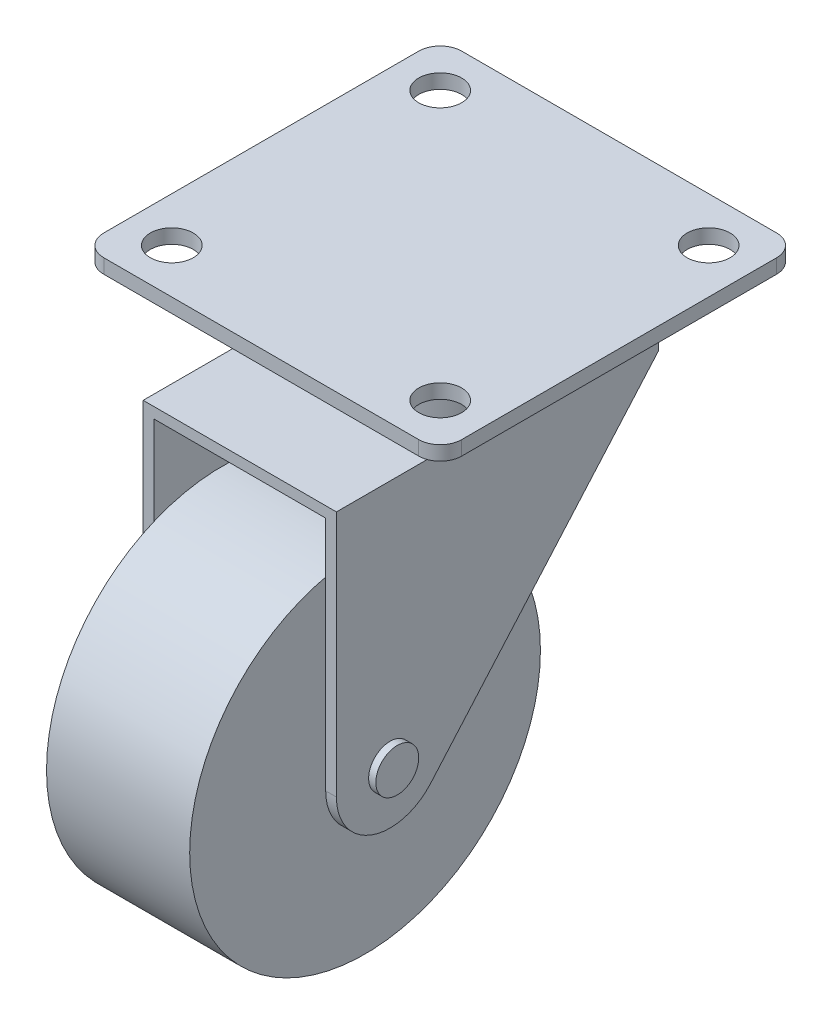
SolidWorks part; units mm, degrees
ref_plane "Front Plane" through (0, 0, 0) normal (0, 0, 1) x (1, 0, 0)
ref_plane "Top Plane" through (0, 0, 0) normal (0, 1, 0) x (1, 0, 0)
ref_plane "Right Plane" through (0, 0, 0) normal (1, 0, 0) x (0, 0, -1)
sketch "Sketch1" plane through (0, 0, 0) normal (0, 1, 0) x (1, 0, 0)
  line L1 (-22, -25) -> (22, -25)
  line L2 (-25, -22) -> (-25, 22)
  line L3 (-22, 25) -> (22, 25)
  line L4 (25, -22) -> (25, 22)
  line L5 (-25, -25) -> (25, 25) construction
  line L6 (-25, 25) -> (25, -25) construction
  line L7 (-18.75, 18.75) -> (18.75, 18.75) construction
  line L8 (-18.75, 18.75) -> (-18.75, -18.75) construction
  line L9 (-18.75, -18.75) -> (18.75, -18.75) construction
  line L10 (18.75, 18.75) -> (18.75, -18.75) construction
  circle A0 centre (18.75, 18.75) radius 3
  circle A1 centre (18.75, -18.75) radius 3
  circle A2 centre (-18.75, -18.75) radius 3
  circle A3 centre (-18.75, 18.75) radius 3
  arc A4 (-25, 22) -> (-22, 25) centre (-22, 22) cw
  arc A5 (-22, -25) -> (-25, -22) centre (-22, -22) cw
  arc A6 (22, -25) -> (25, -22) centre (22, -22) ccw
  arc A7 (22, 25) -> (25, 22) centre (22, 22) cw
  point P0 (0, 0)
  dimension "D2" = 6
  dimension "D4" = 3
  dimension "D1" = 50
  dimension "D3" = 37.5
extrude "Boss-Extrude1" add sketch "Sketch1" against normal blind 2
sketch "Sketch2" plane through (0, 0, 0) normal (0, 0, 1) x (1, 0, 0)
  line L0 (0, -32.5) -> (0, 0) construction
  line L1 (13.5, -53.5) -> (-13.5, -53.5) construction
  line L2 (13.5, -53.5) -> (13.5, -11.5)
  line L3 (13.5, -11.5) -> (-13.5, -11.5)
  line L4 (-13.5, -53.5) -> (-13.5, -11.5)
  line L5 (13.5, -53.5) -> (-13.5, -11.5) construction
  line L6 (13.5, -11.5) -> (-13.5, -53.5) construction
  line L7 (12, -53.5) -> (12, -13)
  line L8 (12, -13) -> (-12, -13)
  line L9 (-12, -53.5) -> (-12, -13)
  line L10 (13.5, -53.5) -> (12, -53.5)
  line L11 (-12, -53.5) -> (-13.5, -53.5)
  line L12 (-22, -2) -> (22, -2) construction
  point P0 (0, -32.5)
  point P12 (13.5, -11.3811)
  dimension "D2" = 42
  dimension "D3" = 27
  dimension "D4" = 9.5
  dimension "D1" = 1.5
sketch "Sketch3" plane through (0, 0, 0) normal (1, 0, 0) x (0, 0, -1)
  line L0 (17, -11.5) -> (17, -14.5)
  line L1 (-28, -11.5) -> (17, -11.5) construction
  line L2 (-28, -11.5) -> (-28, -53.5) construction
  line L3 (-28, -53.5) -> (17, -53.5) construction
  line L4 (17, -11.5) -> (17, -53.5) construction
  line L5 (17, -14.5) -> (-14.8535, -50.9363)
  line L7 (-28, -46) -> (-28, -11.5)
  line L8 (-28, -11.5) -> (17, -11.5)
  arc A0 (-28, -46) -> (-14.8535, -50.9363) centre (-20.5, -46) ccw
  dimension "D3" = 15
  dimension "D1" = 45
  dimension "D2" = 3
  dimension "D4" = 3
extrude "Boss-Extrude2" add sketch "Sketch2" along normal up to vertex (28 mm away) and the other way up to vertex (17 mm away) separate body up to point (0, -11.5, 28) other way up to point (0, -11.5, -17)
extrude "Cut-Extrude1" cut sketch "Sketch3" against normal through all both and the other way through all flip side to cut
sketch "Sketch4" plane through (13.5, 0, 0) normal (1, 0, 0) x (0, 0, -1)
  circle A0 centre (-20.5, -46) radius 3
  dimension "D1" = 6
extrude "Boss-Extrude3" add sketch "Sketch4" along normal blind 1 and the other way offset from surface (28 mm away) 1 other way up to face at (-13.5, -27.7979, 7.7126)
sketch "Sketch5" plane through (0, 0, 0) normal (1, 0, 0) x (0, 0, -1)
  circle A0 centre (-20.5, -46) radius 24.5
  dimension "D1" = 49
extrude "Boss-Extrude4" add sketch "Sketch5" along normal mid plane 20 separate body
sketch "Sketch6" plane through (0, -11.5, 0) normal (0, 1, 0) x (1, 0, 0)
  line L0 (13.5, 0) -> (-13.5, 0) construction
  line L1 (13.5, -28) -> (13.5, 17) construction
  circle A0 centre (0, 0) radius 13.5
  point P4 (0, 0)
extrude "Boss-Extrude5" add sketch "Sketch6" along normal up to surface (9.5 mm away) up to face at (-18.75, -2, -15.75)
